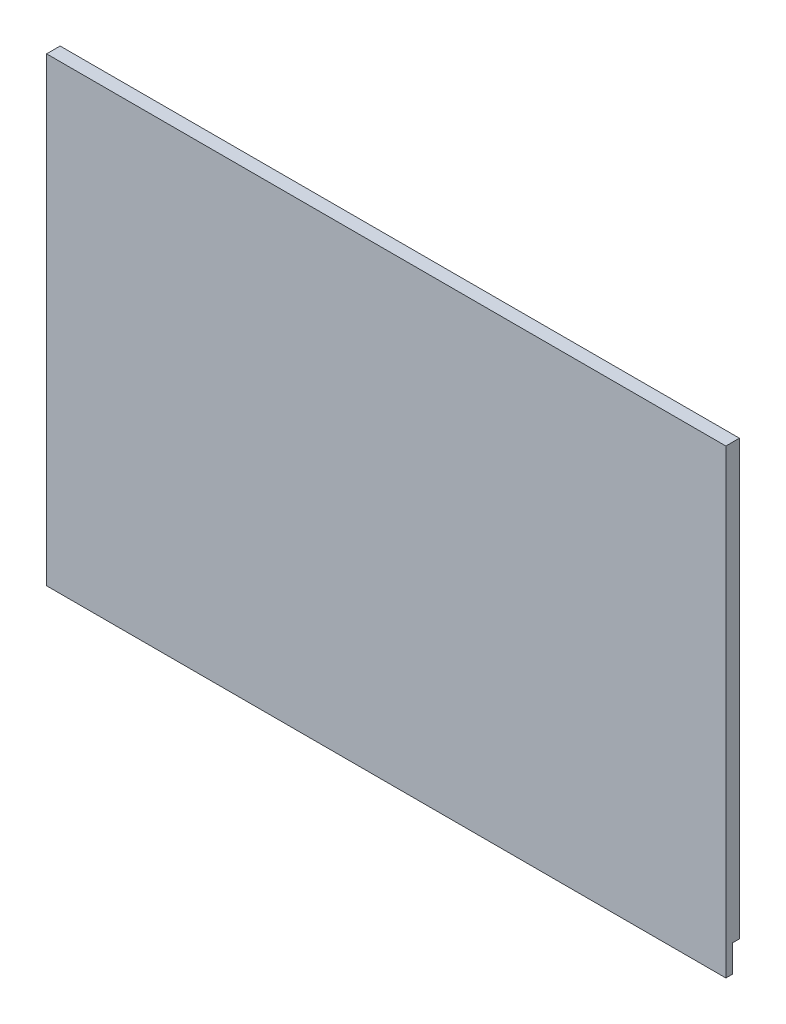
SolidWorks part; units mm, degrees
ref_plane "Front Plane" through (0, 0, 0) normal (0, 0, 1) x (1, 0, 0)
ref_plane "Top Plane" through (0, 0, 0) normal (0, 1, 0) x (1, 0, 0)
ref_plane "Right Plane" through (0, 0, 0) normal (1, 0, 0) x (0, 0, -1)
sketch "Sketch1" plane through (0, 0, 0) normal (0, 0, 1) x (1, 0, 0)
  line L1 (0, 0) -> (-159.1564, 0)
  line L2 (0, 0) -> (0, 107.95)
  line L3 (0, 107.95) -> (-159.1564, 107.95)
  line L4 (-159.1564, 0) -> (-159.1564, 107.95)
  dimension "D1" = 107.95
  dimension "D2" = 159.1564
extrude "Boss-Extrude1" add sketch "Sketch1" along normal blind 3.175
sketch "Sketch2" plane through (0, 0, 0) normal (0, 0, -1) x (-1, 0, 0)
  line L0 (159.1564, 107.95) -> (159.1564, 0) construction
  line L1 (0, 0) -> (159.1564, 0)
  line L2 (0, 0) -> (0, 6.35)
  line L3 (0, 6.35) -> (159.1564, 6.35)
  line L4 (159.1564, 0) -> (159.1564, 6.35)
  dimension "D1" = 6.35
extrude "Cut-Extrude1" cut sketch "Sketch2" against normal blind 1.5875
